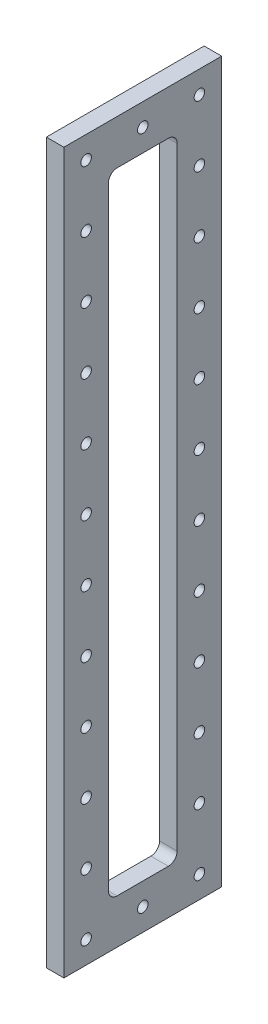
SolidWorks part; units mm, degrees
ref_plane "Plano frontal" through (0, 0, 0) normal (0, 0, 1) x (1, 0, 0)
ref_plane "Plano superior" through (0, 0, 0) normal (0, 1, 0) x (1, 0, 0)
ref_plane "Plano direito" through (0, 0, 0) normal (1, 0, 0) x (0, 0, -1)
sketch "Sketch1" plane through (2615, 0, 0) normal (1, 0, 0) x (0, 0, -1)
  line L0 (-957.3, 807.3) -> (-957.3, 842.3) construction
  line L1 (-970, 1205) -> (-880, 1205)
  line L2 (-970, 1205) -> (-970, 794.6)
  line L3 (-970, 794.6) -> (-880, 794.6)
  line L4 (-880, 1205) -> (-880, 794.6)
  line L5 (-957.3, 1192.3) -> (-892.7, 1192.3) construction
  line L6 (-957.3, 1192.3) -> (-957.3, 807.3) construction
  line L7 (-957.3, 807.3) -> (-892.7, 807.3) construction
  line L8 (-892.7, 1192.3) -> (-892.7, 807.3) construction
  line L9 (-925, 820) -> (-925, 807.3) construction
  line L10 (-939.6, 1179.6) -> (-910.4, 1179.6)
  line L11 (-944.6, 1174.6) -> (-944.6, 825)
  line L12 (-939.6, 820) -> (-910.4, 820)
  line L13 (-905.4, 1174.6) -> (-905.4, 825)
  line L14 (-925, 807.3) -> (-925, 794.6) construction
  line L15 (-957.3, 1122.3) -> (-970, 1122.3) construction
  line L16 (-957.3, 1122.3) -> (-944.6, 1122.3) construction
  line L17 (-925, 1192.3) -> (-925, 1205) construction
  line L18 (-925, 1192.3) -> (-925, 1179.6) construction
  circle A0 centre (-957.3, 807.3) radius 3
  circle A1 centre (-892.7, 807.3) radius 3
  circle A2 centre (-957.3, 842.3) radius 3
  circle A3 centre (-892.7, 842.3) radius 3
  circle A4 centre (-957.3, 877.3) radius 3
  circle A5 centre (-892.7, 877.3) radius 3
  circle A6 centre (-957.3, 912.3) radius 3
  circle A7 centre (-892.7, 912.3) radius 3
  circle A8 centre (-957.3, 947.3) radius 3
  circle A9 centre (-892.7, 947.3) radius 3
  circle A10 centre (-957.3, 982.3) radius 3
  circle A11 centre (-892.7, 982.3) radius 3
  circle A12 centre (-957.3, 1017.3) radius 3
  circle A13 centre (-892.7, 1017.3) radius 3
  circle A14 centre (-957.3, 1052.3) radius 3
  circle A15 centre (-892.7, 1052.3) radius 3
  circle A16 centre (-957.3, 1087.3) radius 3
  circle A17 centre (-892.7, 1087.3) radius 3
  circle A18 centre (-957.3, 1122.3) radius 3
  circle A19 centre (-892.7, 1122.3) radius 3
  circle A20 centre (-957.3, 1157.3) radius 3
  circle A21 centre (-892.7, 1157.3) radius 3
  circle A22 centre (-957.3, 1192.3) radius 3
  circle A23 centre (-892.7, 1192.3) radius 3
  circle A24 centre (-925, 807.3) radius 3
  circle A25 centre (-925, 1192.3) radius 3
  arc A26 (-944.6, 825) -> (-939.6, 820) centre (-939.6, 825) ccw
  arc A27 (-910.4, 820) -> (-905.4, 825) centre (-910.4, 825) ccw
  arc A28 (-905.4, 1174.6) -> (-910.4, 1179.6) centre (-910.4, 1174.6) ccw
  arc A29 (-944.6, 1174.6) -> (-939.6, 1179.6) centre (-939.6, 1174.6) cw
  point P4 (0, 0)
  point P70 (0, 0)
  dimension "D5" = 6
  dimension "D6" = 5
  dimension "D2" = 35
  dimension "D3" = 25.4
  dimension "D4" = 90
  dimension "D7" = 25.4
  dimension "D8" = 25.4
  dimension "D1" = 12
extrude "Boss-Extrude1" add sketch "Sketch1" along normal blind 10
